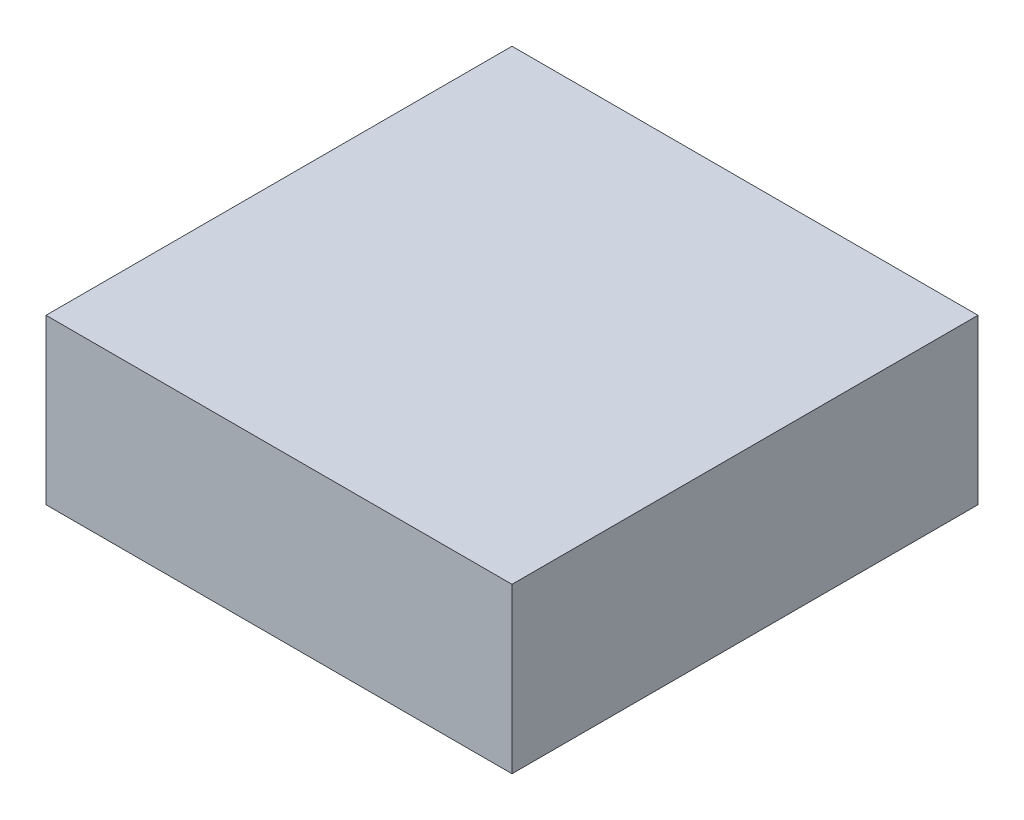
SolidWorks part; units mm, degrees
ref_plane "Front Plane" through (0, 0, 0) normal (0, 0, 1) x (1, 0, 0)
ref_plane "Top Plane" through (0, 0, 0) normal (0, 1, 0) x (1, 0, 0)
ref_plane "Right Plane" through (0, 0, 0) normal (1, 0, 0) x (0, 0, -1)
sketch "Sketch2" plane through (0, 0, 0) normal (0, 1, 0) x (1, 0, 0)
  line L1 (-14.2, 14.2) -> (14.2, 14.2)
  line L2 (-14.2, 14.2) -> (-14.2, -14.2)
  line L3 (-14.2, -14.2) -> (14.2, -14.2)
  line L4 (14.2, 14.2) -> (14.2, -14.2)
  line L5 (-14.2, 14.2) -> (14.2, -14.2) construction
  line L6 (-14.2, -14.2) -> (14.2, 14.2) construction
  point P0 (0, 0)
  dimension "D1" = 28.4
extrude "Boss-Extrude1" add sketch "Sketch2" along normal blind 10
